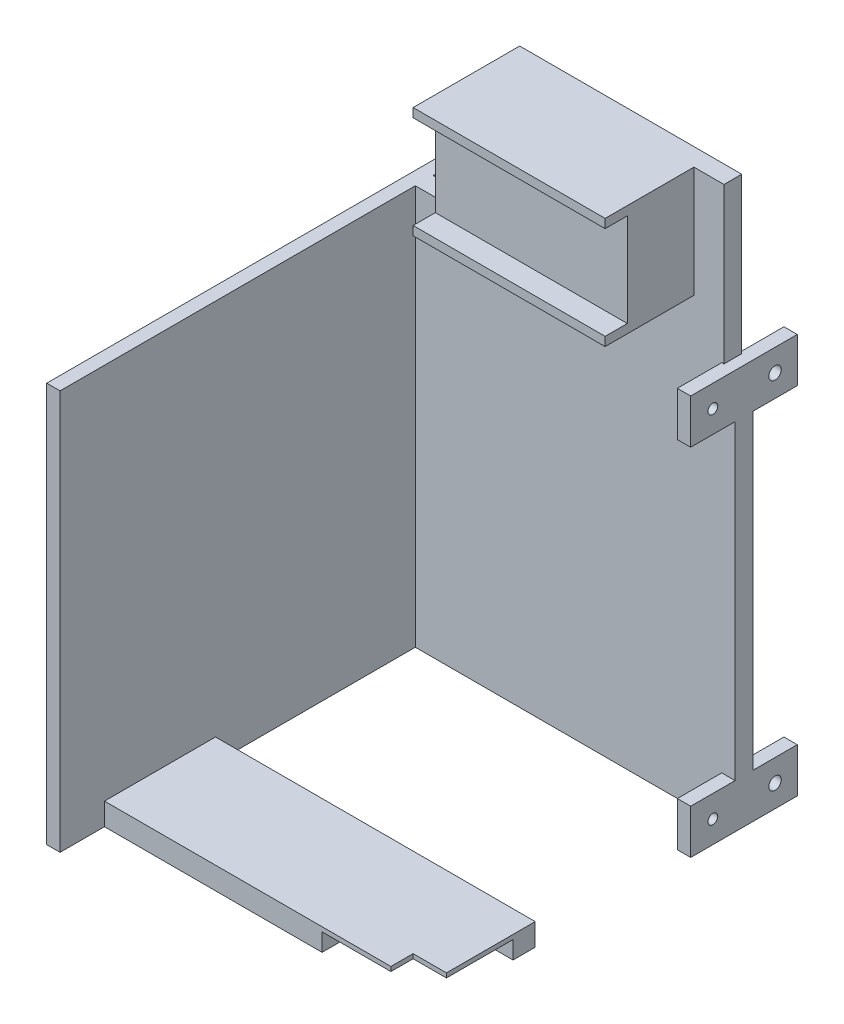
SolidWorks part; units mm, degrees
ref_plane "前基準面" through (0, 0, 0) normal (0, 0, 1) x (1, 0, 0)
ref_plane "上基準面" through (0, 0, 0) normal (0, 1, 0) x (1, 0, 0)
ref_plane "右基準面" through (0, 0, 0) normal (1, 0, 0) x (0, 0, -1)
sketch "草圖1" plane through (0, 0, 0) normal (0, 0, 1) x (1, 0, 0)
  line L0 (0, -55) -> (0, 55) construction
  line L1 (-37.5, 45) -> (-35, 45)
  line L2 (-37.5, 45) -> (-37.5, -45)
  line L3 (-37.5, -45) -> (37.5, -45)
  line L4 (37.5, 45) -> (37.5, -45)
  line L5 (55, 0) -> (-55, 0) construction
  line L6 (15, 45) -> (37.5, 45)
  line L8 (-35, 45) -> (-35, 80)
  line L9 (-35, 80) -> (15, 80)
  line L10 (15, 45) -> (15, 80)
  dimension "D1" = 75
  dimension "D2" = 90
  dimension "D3" = 37.5
  dimension "D4" = 45
  dimension "D5" = 35
  dimension "D6" = 35
  dimension "D7" = 50
extrude "填料-伸長1" add sketch "草圖1" along normal blind 4 contours L1 L10 L9 L8 | L4 L1 L2 L3
sketch "草圖3" plane through (0, 0, 4) normal (0, 0, 1) x (1, 0, 0)
  line L0 (-35, 80) -> (15, 80) construction
  line L1 (-28.2355, 57) -> (15, 57)
  line L2 (-28.2355, 57) -> (-28.2355, 55)
  line L3 (-28.2355, 55) -> (15, 55)
  line L4 (15, 57) -> (15, 55)
  line L5 (-28.2355, 80) -> (15, 80)
  line L6 (-28.2355, 80) -> (-28.2355, 78)
  line L7 (-28.2355, 78) -> (15, 78)
  line L8 (15, 80) -> (15, 78)
  dimension "D1" = 2
  dimension "D2" = 2
  dimension "D3" = 21
extrude "填料-伸長2" add sketch "草圖3" along normal blind 20
sketch "草圖4" plane through (0, 0, 4) normal (0, 0, 1) x (1, 0, 0)
  line L1 (-28.2355, 78) -> (15, 78)
  line L2 (-28.2355, 78) -> (-28.2355, 57)
  line L3 (-28.2355, 57) -> (15, 57)
  line L4 (15, 78) -> (15, 57)
extrude "填料-伸長3" add sketch "草圖4" along normal blind 15
sketch "草圖8" plane through (0, 0, 0) normal (0, 0, -1) x (-1, 0, 0)
  line L1 (-37.5, 45) -> (-34.5, 45)
  line L2 (-37.5, 45) -> (-37.5, 35)
  line L3 (-37.5, 35) -> (-34.5, 35)
  line L4 (-34.5, 45) -> (-34.5, 35)
  line L5 (37.5, 45) -> (34.5, 45)
  line L6 (37.5, 45) -> (37.5, 35)
  line L7 (37.5, 35) -> (34.5, 35)
  line L8 (34.5, 45) -> (34.5, 35)
  line L9 (37.5, -45) -> (34.5, -45)
  line L10 (37.5, -45) -> (37.5, -35)
  line L11 (37.5, -35) -> (34.5, -35)
  line L12 (34.5, -45) -> (34.5, -35)
  line L13 (-37.5, -45) -> (-34.5, -45)
  line L14 (-37.5, -45) -> (-37.5, -35)
  line L15 (-37.5, -35) -> (-34.5, -35)
  line L16 (-34.5, -45) -> (-34.5, -35)
  dimension "D1" = 3
  dimension "D2" = 3
  dimension "D3" = 10
  dimension "D4" = 10
  dimension "D5" = 10
  dimension "D6" = 3
  dimension "D7" = 10
  dimension "D8" = 3
extrude "填料-伸長4" add sketch "草圖8" along normal blind 10
sketch "草圖10" plane through (37.5, 0, 0) normal (1, 0, 0) x (0, 0, -1)
  line L0 (10, 45) -> (10, 35) construction
  line L1 (-4, 45) -> (10, 45) construction
  line L2 (10, -35) -> (0, -35) construction
  line L3 (10, -35) -> (10, -45) construction
  circle A0 centre (5, 40) radius 1.4
  circle A1 centre (5, -40) radius 1.4
  dimension "D1" = 2.8
  dimension "D4" = 2.8
  dimension "D2" = 5
  dimension "D3" = 5
  dimension "D5" = 5
  dimension "D6" = 5
extrude "除料-伸長1" cut sketch "草圖10" against normal blind 83
sketch "草圖11" plane through (0, 0, 4) normal (0, 0, 1) x (1, 0, 0)
  line L5 (37.5, 45) -> (34.5, 45)
  line L6 (37.5, 45) -> (37.5, -45)
  line L7 (37.5, -45) -> (34.5, -45)
  line L8 (34.5, 45) -> (34.5, -45)
extrude "填料-伸長5" add sketch "草圖11" along normal blind 80
sketch "草圖12" plane through (0, -45, 0) normal (0, -1, 0) x (1, 0, 0)
  line L0 (37.5, 84) -> (37.5, -10) construction
  line L2 (-37.5, 74) -> (-37.5, 49)
  line L3 (-37.5, 49) -> (37.5, 49)
  line L4 (37.5, 74) -> (37.5, 49)
  line L6 (-37.5, 74) -> (37.5, 74)
  dimension "D1" = 25
  dimension "D2" = 75
  dimension "D3" = 0
extrude "填料-伸長6" add sketch "草圖12" against normal blind 5
sketch "草圖13" plane through (0, -45, 0) normal (0, -1, 0) x (1, 0, 0)
  line L0 (34.5, 74) -> (-37.5, 74) construction
  line L1 (-37.5, 74) -> (-14.5, 74)
  line L2 (-37.5, 74) -> (-37.5, 54)
  line L3 (-37.5, 54) -> (-14.5, 54)
  line L4 (-14.5, 74) -> (-14.5, 54)
  line L6 (-37.5, 74) -> (-37.5, 49) construction
  dimension "D1" = 20
  dimension "D2" = 23
  dimension "D3" = 0
extrude "除料-伸長2" cut sketch "草圖13" against normal blind 4
sketch "草圖14" plane through (0, -41, 0) normal (0, -1, 0) x (1, 0, 0)
  line L0 (-14.5, 74) -> (-37.5, 74) construction
  line L1 (-37.5, 74) -> (-30, 74)
  line L2 (-37.5, 74) -> (-37.5, 69)
  line L3 (-37.5, 69) -> (-30, 69)
  line L4 (-30, 74) -> (-30, 69)
  line L7 (-37.5, 74) -> (-37.5, 54) construction
  dimension "D1" = 5
  dimension "D2" = 7.5
  dimension "D3" = 0
extrude "除料-伸長3" cut sketch "草圖14" against normal up to next
sketch "草圖15" plane through (15, 0, 0) normal (1, 0, 0) x (0, 0, -1)
  line L0 (-24, 78) -> (-19, 78) construction
  line L1 (-19, 57) -> (-19, 78) construction
  line L3 (-24, 57) -> (-19, 57) construction
  circle A0 centre (-16.1, 72.2) radius 1.1
  circle A1 centre (-16.1, 62.8) radius 1.1
  dimension "D1" = 5.8
  dimension "D2" = 2.9
  dimension "D3" = 2.9
  dimension "D4" = 5.8
extrude "除料-伸長4" cut sketch "草圖15" against normal blind 10
sketch "草圖17" plane through (0, 0, 4) normal (0, 0, 1) x (1, 0, 0)
  line L1 (-37.5, 45) -> (-34.5, 45)
  line L2 (-37.5, 45) -> (-37.5, 35)
  line L3 (-37.5, 35) -> (-34.5, 35)
  line L4 (-34.5, 45) -> (-34.5, 35)
  dimension "D1" = 3
  dimension "D2" = 10
extrude "填料-伸長7" add sketch "草圖17" along normal blind 10
sketch "草圖18" plane through (-37.5, 0, 0) normal (-1, 0, 0) x (0, 0, 1)
  line L0 (14, 45) -> (14, 35) construction
  line L1 (14, 45) -> (-10, 45) construction
  circle A0 centre (9, 40) radius 1.1
  dimension "D1" = 5
  dimension "D2" = 5
extrude "除料-伸長5" cut sketch "草圖18" against normal blind 3 contours A0
sketch "草圖19" plane through (0, 0, 4) normal (0, 0, 1) x (1, 0, 0)
  line L0 (-37.5, 35) -> (-37.5, -45) construction
  line L1 (-37.5, -35) -> (-34.5, -35)
  line L2 (-37.5, -35) -> (-37.5, -45)
  line L3 (-37.5, -45) -> (-34.5, -45)
  line L4 (-34.5, -35) -> (-34.5, -45)
  line L5 (-37.5, -45) -> (34.5, -45) construction
  dimension "D1" = 10
  dimension "D2" = 3
extrude "填料-伸長8" add sketch "草圖19" along normal blind 10
sketch "草圖20" plane through (-37.5, 0, 0) normal (-1, 0, 0) x (0, 0, 1)
  line L0 (14, -35) -> (4, -35) construction
  line L1 (14, -35) -> (14, -45) construction
  circle A0 centre (9, -40) radius 1.1
  dimension "D1" = 5
  dimension "D2" = 5
extrude "除料-伸長6" cut sketch "草圖20" against normal blind 3
mirror "鏡射1" about plane through (37.5, 0, 4) normal (1, 0, 0) of bodies 114
delete or keep bodies "本體-刪除/保留 1" type delete bodies bodies 114
